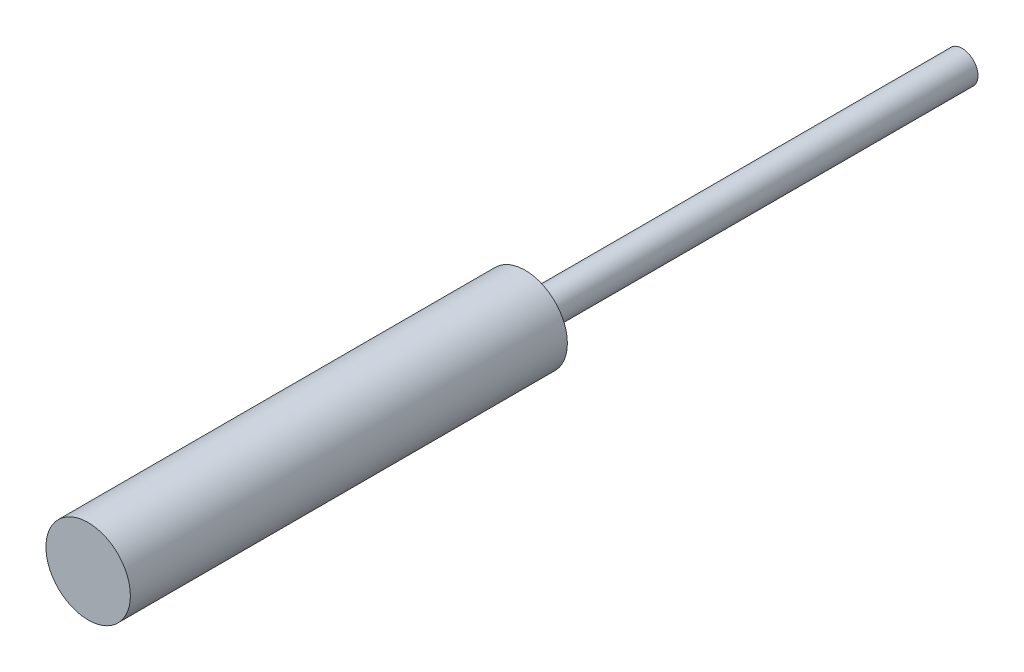
SolidWorks part; units mm, degrees
ref_plane "前视基准面" through (0, 0, 0) normal (0, 0, 1) x (1, 0, 0)
ref_plane "上视基准面" through (0, 0, 0) normal (0, 1, 0) x (1, 0, 0)
ref_plane "右视基准面" through (0, 0, 0) normal (1, 0, 0) x (0, 0, -1)
sketch "草图1" plane through (0, 0, 0) normal (0, 0, 1) x (1, 0, 0)
  circle A0 centre (0, 0) radius 2
  dimension "D1" = 4
extrude "凸台-拉伸1" add sketch "草图1" along normal blind 20.7
sketch "草图2" plane through (0, 0, 0) normal (0, 0, -1) x (-1, 0, 0)
  circle A0 centre (0, 0) radius 0.75
  dimension "D1" = 1.5
extrude "凸台-拉伸2" add sketch "草图2" along normal blind 20.7
